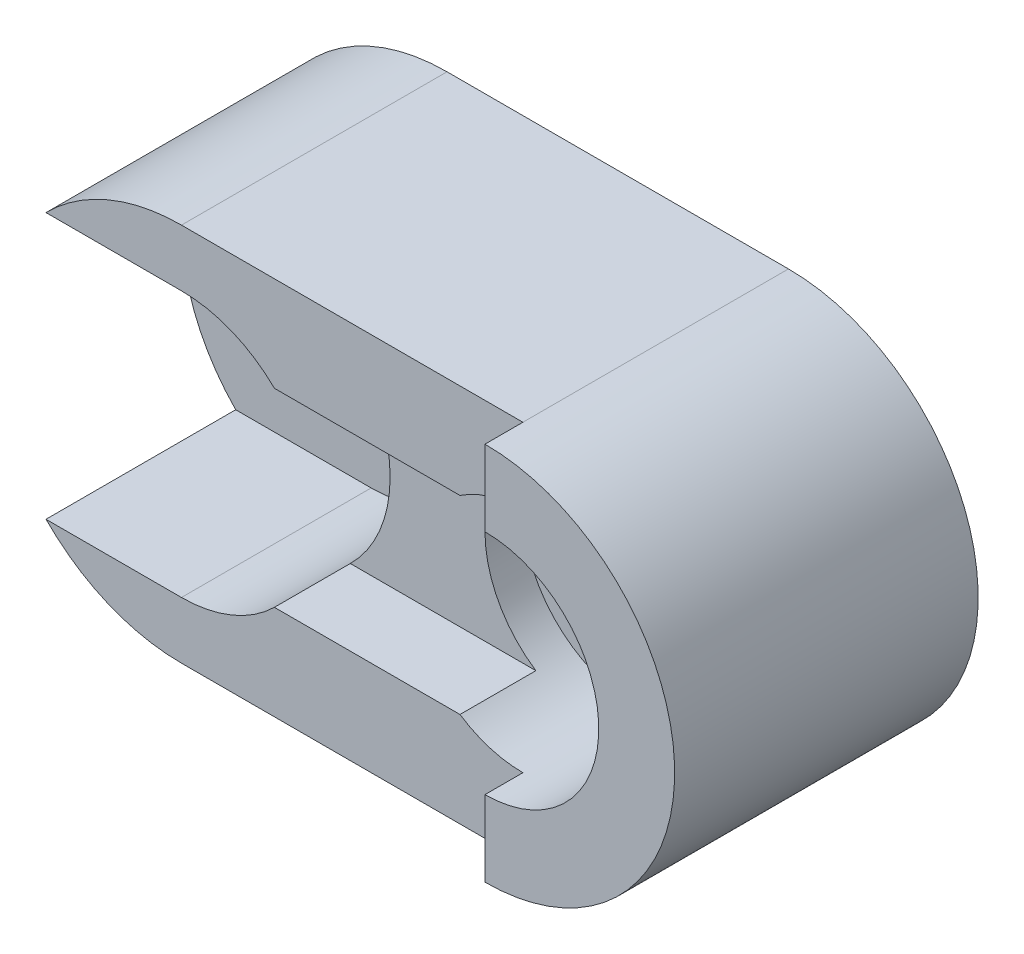
SolidWorks part; units mm, degrees
ref_plane "Front Plane" through (0, 0, 0) normal (0, 0, 1) x (1, 0, 0)
ref_plane "Top Plane" through (0, 0, 0) normal (0, 1, 0) x (1, 0, 0)
ref_plane "Right Plane" through (0, 0, 0) normal (1, 0, 0) x (0, 0, -1)
sketch "Sketch1" plane through (0, 0, 0) normal (0, 0, 1) x (1, 0, 0)
  line L0 (0, 50) -> (90, 50)
  line L1 (0, -50) -> (90, -50)
  arc A0 (0, 50) -> (0, -50) centre (0, 0) ccw
  arc A1 (90, 50) -> (90, -50) centre (90, 0) cw
  dimension "D1" = 50
  dimension "D2" = 50
  dimension "D3" = 90
  dimension "D4" = 90
extrude "Boss-Extrude1" add sketch "Sketch1" along normal blind 70
sketch "Sketch2" plane through (0, 0, 70) normal (0, 0, 1) x (1, 0, 0)
  line L0 (0, -50) -> (90, -50) construction
  line L1 (90, 50) -> (90, 30)
  line L2 (90, -30) -> (90, -50)
  arc A0 (90, 50) -> (90, -50) centre (90, 0) cw
  arc A1 (90, 30) -> (90, -30) centre (90, 0) cw
  dimension "D3" = 30
  dimension "D1" = 20
  dimension "D2" = 20
extrude "Boss-Extrude2" add sketch "Sketch2" along normal blind 10
sketch "Sketch3" plane through (0, 0, 70) normal (0, 0, 1) x (1, 0, 0)
  circle A0 centre (90, 0) radius 30
  dimension "D1" = 60
extrude "Cut-Extrude1" cut sketch "Sketch3" against normal blind 30
sketch "Sketch4" plane through (0, 0, 40) normal (0, 0, 1) x (1, 0, 0)
  circle A0 centre (90, 0) radius 10
  dimension "D1" = 20
extrude "Cut-Extrude2" cut sketch "Sketch4" against normal blind 71
sketch "Sketch5" plane through (0, 0, 70) normal (0, 0, 1) x (1, 0, 0)
  line L0 (0, 35) -> (-35.7071, 35)
  line L1 (0, -35) -> (-35.7071, -35)
  arc A0 (-35.7071, 35) -> (-35.7071, -35) centre (0, 0) ccw
  arc A2 (0, 35) -> (0, -35) centre (0, 0) cw
  arc A6 (0, 50) -> (0, -50) centre (0, 0) ccw construction
  dimension "D3" = 35
  dimension "D1" = 35
  dimension "D2" = 35
  dimension "D4" = 35.7071
extrude "Cut-Extrude6" cut sketch "Sketch5" against normal blind 50
sketch "Sketch9" plane through (0, 0, 20) normal (0, 0, 1) x (1, 0, 0)
  circle A0 centre (0, 0) radius 20
  dimension "D1" = 40
extrude "Cut-Extrude7" cut sketch "Sketch9" against normal blind 50
sketch "Sketch10" plane through (0, 0, 70) normal (0, 0, 1) x (1, 0, 0)
  line L0 (73.4169, 25) -> (24.4949, 25)
  line L1 (73.4169, -25) -> (24.4949, -25)
  arc A2 (24.4949, 25) -> (24.4949, -25) centre (0, 0) cw
  arc A3 (73.4169, 25) -> (73.4169, -25) centre (90, 0) ccw
  arc A4 (73.4169, 25) -> (73.4169, -25) centre (90, 0) ccw
  arc M2 (0, 35) -> (0, -35) centre (0, 0) cw
  arc M7 (90, -30) -> (90, 30) centre (90, 0) cw
  dimension "D1" = 48.922
  dimension "D2" = 35
  dimension "D3" = 30
  dimension "D4" = 48.922
extrude "Cut-Extrude8" cut sketch "Sketch10" against normal blind 20 contours L1 L0 M7 M2
